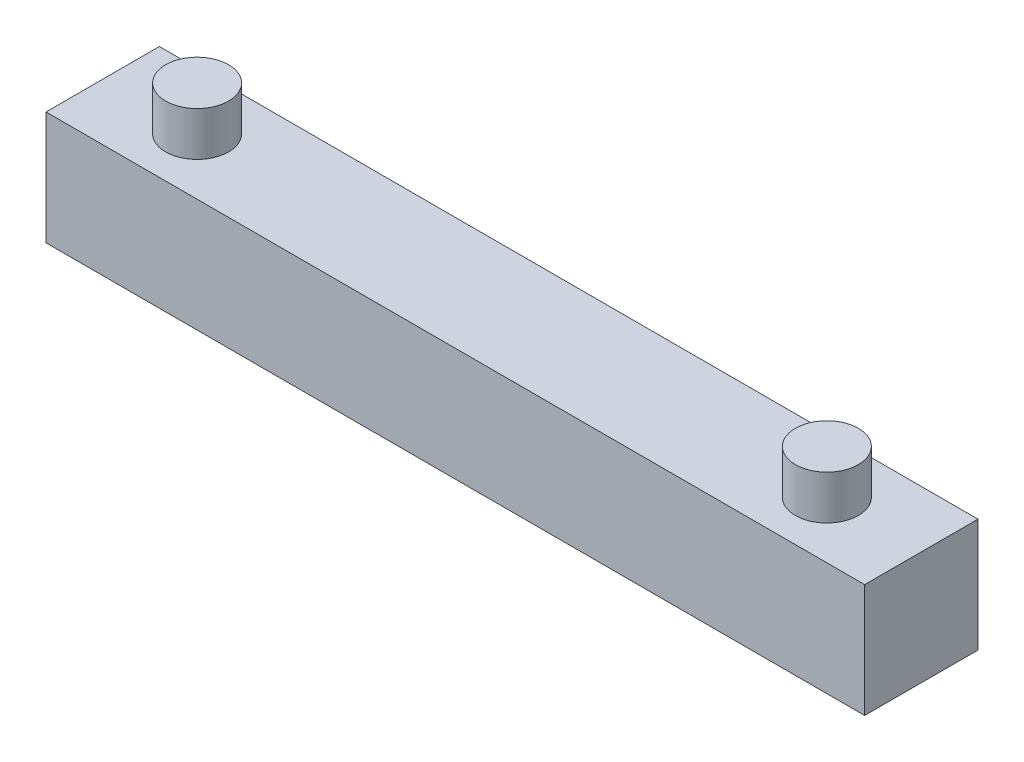
SolidWorks part; units mm, degrees
ref_plane "Front Plane" through (0, 0, 0) normal (0, 0, 1) x (1, 0, 0)
ref_plane "Top Plane" through (0, 0, 0) normal (0, 1, 0) x (1, 0, 0)
ref_plane "Right Plane" through (0, 0, 0) normal (1, 0, 0) x (0, 0, -1)
sketch "Sketch1" plane through (0, 0, 0) normal (0, 1, 0) x (1, 0, 0)
  line L0 (0, 0) -> (65, 0)
  line L1 (65, 0) -> (65, 9)
  line L2 (65, 9) -> (0, 9)
  line L3 (0, 9) -> (0, 0)
  dimension "D1" = 65
  dimension "D2" = 9
extrude "Boss-Extrude1" add sketch "Sketch1" along normal blind 9
sketch "Sketch2" plane through (0, 9, 0) normal (0, 1, 0) x (1, 0, 0)
  line L0 (0, 0) -> (65, 0) construction
  line L1 (0, 9) -> (0, 0) construction
  circle A0 centre (7.5, 4.5) radius 2.5
  circle A1 centre (57.5, 4.5) radius 2.5
  point P6 (0, 4.5)
  dimension "D1" = 5
  dimension "D2" = 4.5
  dimension "D3" = 7.5
  dimension "D4" = 50
extrude "Boss-Extrude2" add sketch "Sketch2" along normal blind 3.5
